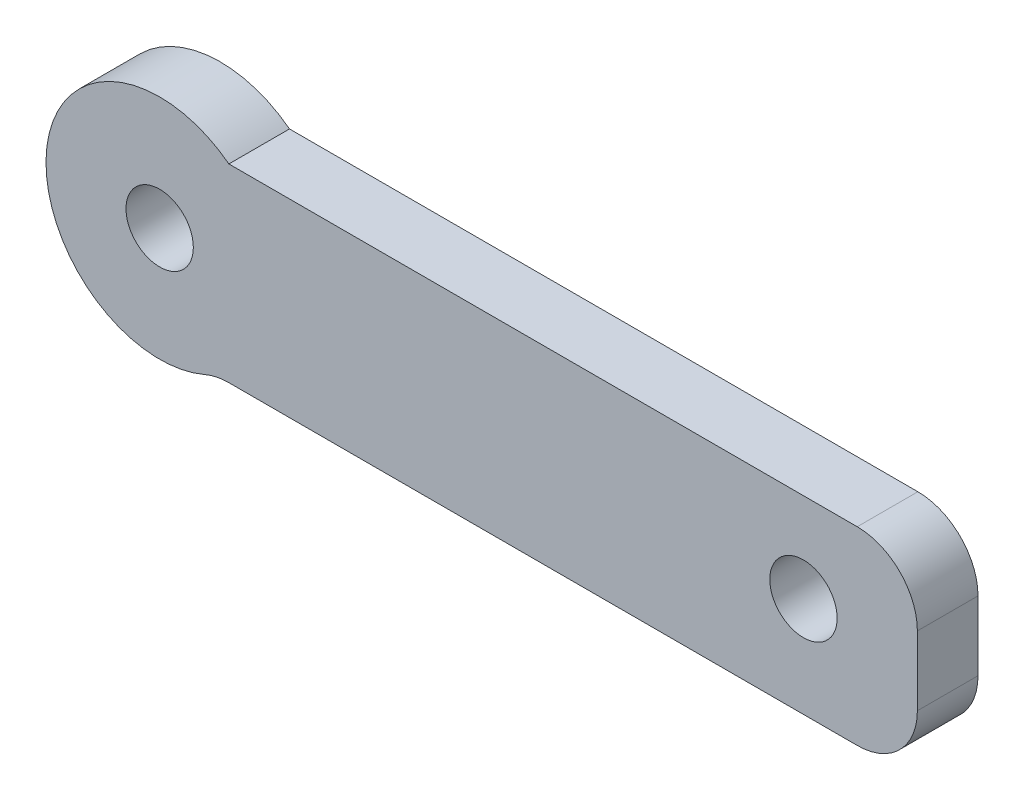
SolidWorks part; units mm, degrees
material "6061-T4 (SS)"
ref_plane "Front Plane" through (0, 0, 0) normal (0, 0, 1) x (1, 0, 0)
ref_plane "Top Plane" through (0, 0, 0) normal (0, 1, 0) x (1, 0, 0)
ref_plane "Right Plane" through (0, 0, 0) normal (1, 0, 0) x (0, 0, -1)
sketch "Sketch1" plane through (0, 0, 0) normal (0, 0, 1) x (1, 0, 0)
  line L1 (1.827, -2.6205) -> (18.4125, -2.6205)
  line L3 (1.827, 2.3795) -> (18.4125, 2.3795)
  line L4 (20, -1.033) -> (20, 0.792)
  arc A0 (1.827, 2.3795) -> (1.1948, -2.7518) centre (0, 0) ccw
  arc A1 (1.827, -2.6205) -> (1.1948, -2.7518) centre (1.827, -4.208) ccw
  arc A3 (18.4125, -2.6205) -> (20, -1.033) centre (18.4125, -1.033) ccw
  arc A4 (18.4125, 2.3795) -> (20, 0.792) centre (18.4125, 0.792) cw
  point P12 (20, -2.6205)
  point P15 (20, 2.3795)
  dimension "D2" = 6
  dimension "D4" = 1.5875
  dimension "D5" = 1.5875
  dimension "D1" = 20
  dimension "D3" = 5
extrude "Boss-Extrude1" add sketch "Sketch1" along normal blind 1.6002
hole_wizard "#0 Clearance Hole1" positions "Sketch2" profile "Sketch3" hole size "#0" standard "ANSI Inch"
sketch "Sketch2" plane through (0, 0, 1.6002) normal (0, 0, 1) x (1, 0, 0)
  arc A0 (1.827, 2.3795) -> (1.1948, -2.7518) centre (0, 0) ccw construction
  point P0 (0, 0)
sketch "Sketch3" plane through (0, 0, 1.6002) normal (1, 0, 0) x (0, -1, 0)
  line L0 (0, 0) -> (0, 465.5342)
  line L1 (0, 465.5342) -> (0.889, 465)
  line L2 (0.889, 465) -> (0.889, 0)
  line L5 (0.889, 0) -> (0, 0)
  line L10 (0, 465.5342) -> (-0.889, 465) construction
  line L11 (0, -6.35) -> (0, 107.95) construction
  dimension "Hole Dia." = 1.778
  dimension "Hole Depth" = 465
  dimension "Drill Angle" = 118
sketch "Sketch7" plane through (0, 0, 0) normal (0, 0, -1) x (-1, 0, 0)
  line L0 (-8.6344, 0) -> (0, 0)
sketch "Sketch8" plane through (0, 0, 1.6002) normal (0, 0, 1) x (1, 0, 0)
  line L0 (0, -16.9706) -> (16.9932, 0.0227) construction
  line L1 (8.6344, 0) -> (0, 0) construction
  dimension "D1" = 45
hole_wizard "#0 Clearance Hole2" positions "Sketch9" profile "Sketch10" hole size "#0" standard "ANSI Inch"
sketch "Sketch9" plane through (0, 0, 0) normal (0, 0, -1) x (-1, 0, 0)
  point P0 (-16.9932, 0.0227)
sketch "Sketch10" plane through (16.9932, 0.0227, 0) normal (1, 0, 0) x (0, 1, 0)
  line L0 (0, 0) -> (0, 465.5342)
  line L1 (0, 465.5342) -> (0.889, 465)
  line L2 (0.889, 465) -> (0.889, 0)
  line L5 (0.889, 0) -> (0, 0)
  line L10 (0, 465.5342) -> (-0.889, 465) construction
  line L11 (0, -6.35) -> (0, 107.95) construction
  dimension "Hole Dia." = 1.778
  dimension "Hole Depth" = 465
  dimension "Drill Angle" = 118
